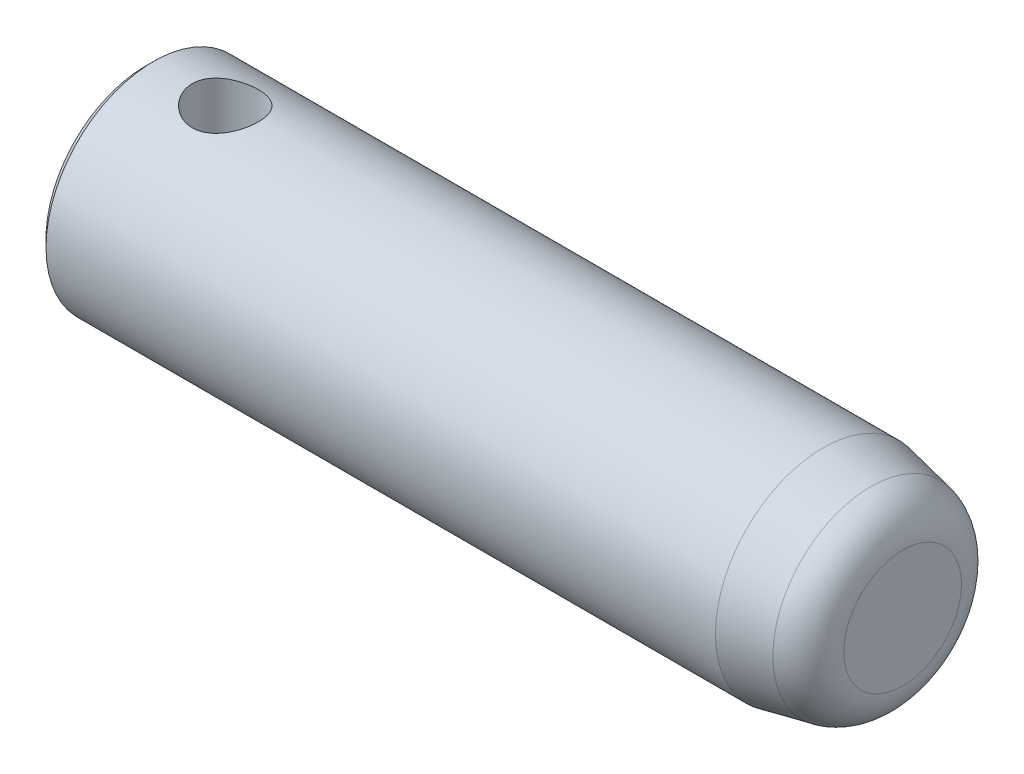
SolidWorks part; units mm, degrees
ref_plane "Front Plane" through (0, 0, 0) normal (0, 0, 1) x (1, 0, 0)
ref_plane "Top Plane" through (0, 0, 0) normal (0, 1, 0) x (1, 0, 0)
ref_plane "Right Plane" through (0, 0, 0) normal (1, 0, 0) x (0, 0, -1)
sketch "Sketch2" plane through (0, 0, 0) normal (1, 0, 0) x (0, 0, -1)
  circle A0 centre (0, 0) radius 13.5
  dimension "D1" = 27
extrude "Boss-Extrude1" add sketch "Sketch2" along normal blind 95
chamfer "Chamfer1" distance 10 angle 11.5 1 edges at (95, 0, -13.5)
fillet "Fillet1" radius 5 1 edges at (95, 0, -11.4655)
chamfer "Chamfer2" distance 1 1 edges at (0, 0, -13.5)
sketch "Sketch3" plane through (0, 0, 0) normal (0, 1, 0) x (1, 0, 0)
  line L0 (0, 0) -> (85, 0) construction
  line L1 (0, 12.5) -> (0, -12.5) construction
  line L2 (85, 13.5) -> (85, -13.5) construction
  circle A0 centre (10, 0) radius 4.15
  dimension "D1" = 8.3
  dimension "D2" = 10
extrude "Cut-Extrude1" cut sketch "Sketch3" against normal through all both and the other way through all
